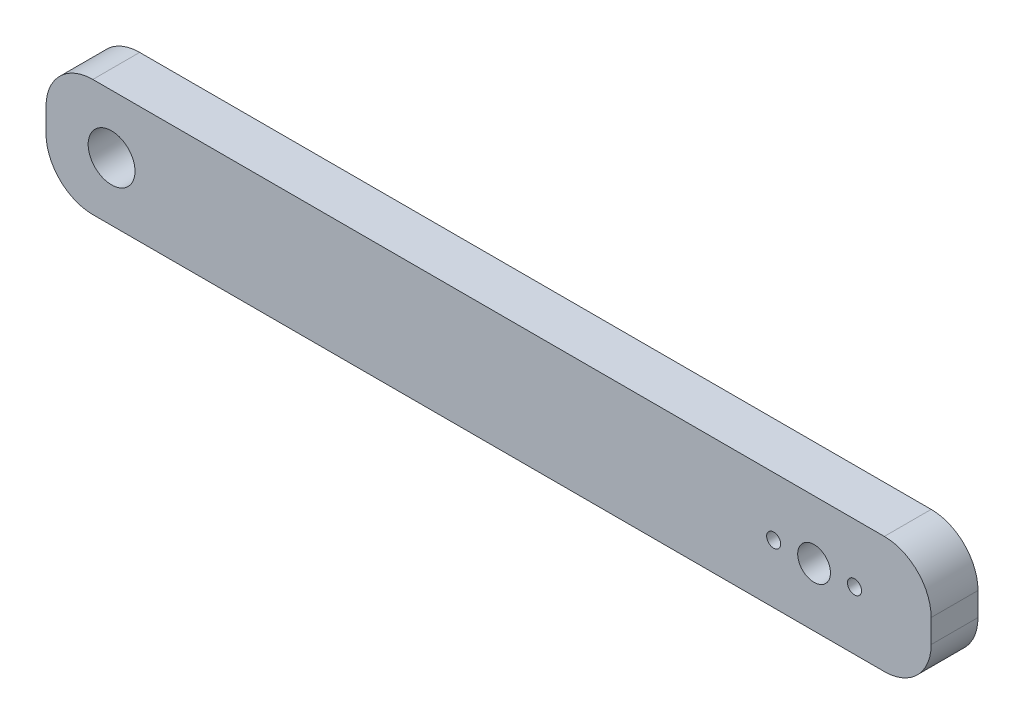
SolidWorks part; units mm, degrees
ref_plane "Front Plane" through (0, 0, 0) normal (0, 0, 1) x (1, 0, 0)
ref_plane "Top Plane" through (0, 0, 0) normal (0, 1, 0) x (1, 0, 0)
ref_plane "Right Plane" through (0, 0, 0) normal (1, 0, 0) x (0, 0, -1)
sketch "Sketch1" plane through (0, 0, 0) normal (0, 0, 1) x (1, 0, 0)
  line L0 (0, 0) -> (-90.8475, 0)
  line L1 (-100.8475, -10) -> (-100.8475, -15)
  line L2 (-90.8475, -25) -> (78.1525, -25)
  line L3 (88.1525, -15) -> (88.1525, -10)
  line L4 (78.1525, 0) -> (0, 0)
  arc A0 (88.1525, -10) -> (78.1525, 0) centre (78.1525, -10) ccw
  arc A1 (88.1525, -15) -> (78.1525, -25) centre (78.1525, -15) cw
  arc A2 (-100.8475, -15) -> (-90.8475, -25) centre (-90.8475, -15) ccw
  arc A3 (-100.8475, -10) -> (-90.8475, 0) centre (-90.8475, -10) cw
  circle A4 centre (-86.8475, -12.5) radius 5
  circle A5 centre (63.1525, -12.5) radius 3.5
  circle A6 centre (54.5225, -12.5) radius 1.5
  circle A7 centre (71.7825, -12.5) radius 1.5
  point P21 (63.1525, -12.5)
  point P23 (0, 0)
  point P24 (0, 0)
  point P25 (0, 0)
  point P26 (0, 0)
  dimension "D2" = 10
  dimension "D3" = 10
  dimension "D5" = 150
  dimension "D7" = 8.63
  dimension "D1" = 25
  dimension "D4" = 14
  dimension "D6" = 25
  dimension "D8" = 8.63
  dimension "D9" = 189
extrude "Boss-Extrude1" add sketch "Sketch1" along normal blind 10
